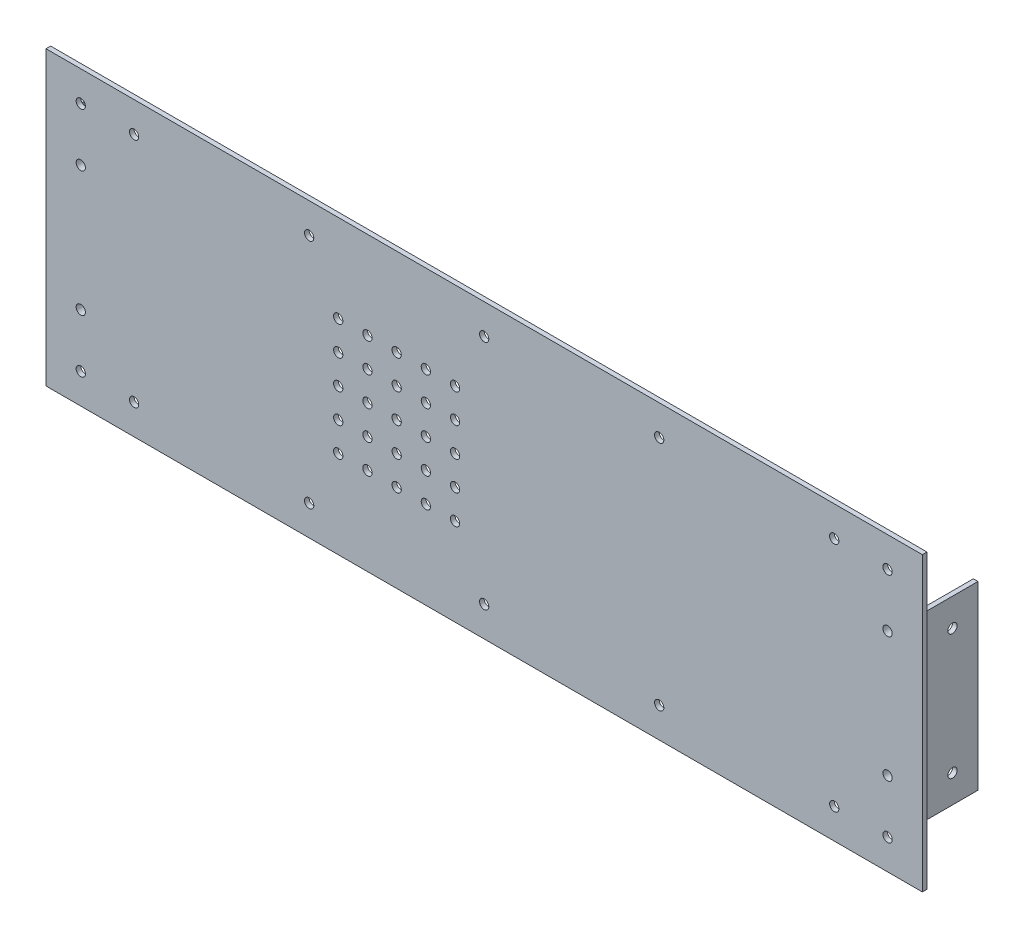
SolidWorks part; units mm, degrees
ref_plane "Plan de face" through (0, 0, 0) normal (0, 0, 1) x (1, 0, 0)
ref_plane "Plan de dessus" through (0, 0, 0) normal (0, 1, 0) x (1, 0, 0)
ref_plane "Plan de droite" through (0, 0, 0) normal (1, 0, 0) x (0, 0, -1)
sketch "Esquisse1" plane through (0, 0, 0) normal (0, 0, 1) x (1, 0, 0)
  line L1 (-120.1017, 81.1475) -> (179.8983, 81.1475)
  line L2 (-120.1017, 81.1475) -> (-120.1017, -18.8525)
  line L3 (-120.1017, -18.8525) -> (179.8983, -18.8525)
  line L4 (179.8983, 81.1475) -> (179.8983, -18.8525)
  dimension "D1" = 300
  dimension "D2" = 100
extrude "Boss.-Extru.1" add sketch "Esquisse1" along normal blind 1.5875
sketch "Esquisse2" plane through (0, 0, 0) normal (0, 0, -1) x (-1, 0, 0)
  line L1 (99.4642, 62.0975) -> (118.5142, 62.0975)
  line L2 (99.4642, 62.0975) -> (99.4642, 0.1975)
  line L3 (99.4642, 0.1975) -> (118.5142, 0.1975)
  line L4 (118.5142, 62.0975) -> (118.5142, 0.1975)
  line L5 (-178.3108, 62.0975) -> (-159.2608, 62.0975)
  line L6 (-178.3108, 62.0975) -> (-178.3108, 0.1975)
  line L7 (-178.3108, 0.1975) -> (-159.2608, 0.1975)
  line L8 (-159.2608, 62.0975) -> (-159.2608, 0.1975)
  line L10 (-179.8983, 81.1475) -> (120.1017, 81.1475) construction
  line L11 (-159.2608, 62.0975) -> (-159.2608, 81.1475) construction
  line L12 (-159.2608, 0.1975) -> (-159.2608, -18.8525) construction
  line L13 (120.1017, -18.8525) -> (-179.8983, -18.8525) construction
  line L14 (120.1017, 81.1475) -> (120.1017, -18.8525) construction
  line L15 (-179.8983, -18.8525) -> (-179.8983, 81.1475) construction
  dimension "D1" = 19.05
  dimension "D2" = 19.05
  dimension "D3" = 1.5875
  dimension "D4" = 1.5875
extrude "Boss.-Extru.2" add sketch "Esquisse2" along normal blind 1.5875
sketch "Esquisse3" plane through (0, 0, -1.5875) normal (0, 0, -1) x (-1, 0, 0)
  line L0 (118.5142, 0.1975) -> (118.5142, 62.0975) construction
  line L1 (-178.3108, 62.0975) -> (-176.7233, 62.0975)
  line L2 (-178.3108, 62.0975) -> (-178.3108, 0.1975)
  line L3 (-178.3108, 0.1975) -> (-176.7233, 0.1975)
  line L4 (-176.7233, 62.0975) -> (-176.7233, 0.1975)
  line L5 (116.9267, 62.0975) -> (118.5142, 62.0975)
  line L6 (116.9267, 62.0975) -> (116.9267, 0.1975)
  line L7 (116.9267, 0.1975) -> (118.5142, 0.1975)
  line L8 (118.5142, 62.0975) -> (118.5142, 0.1975)
  line L9 (118.5142, 62.0975) -> (99.4642, 62.0975) construction
  line L10 (99.4642, 0.1975) -> (118.5142, 0.1975) construction
  line L11 (-178.3108, 62.0975) -> (-178.3108, 0.1975) construction
  line L12 (-159.2608, 62.0975) -> (-178.3108, 62.0975) construction
  line L13 (-178.3108, 0.1975) -> (-159.2608, 0.1975) construction
  dimension "D1" = 1.5875
extrude "Boss.-Extru.3" add sketch "Esquisse3" along normal blind 17.4625
sketch "Esquisse4" plane through (0, 0, -1.5875) normal (0, 0, -1) x (-1, 0, 0)
  line L0 (-176.7233, 14.7337) -> (-159.2608, 14.7337) construction
  line L1 (-176.7233, 0.1975) -> (-176.7233, 62.0975) construction
  line L2 (-159.2608, 0.1975) -> (-159.2608, 62.0975) construction
  line L3 (99.4642, 15.3602) -> (116.9267, 15.3602) construction
  line L4 (99.4642, 62.0975) -> (99.4642, 0.1975) construction
  line L5 (116.9267, 62.0975) -> (116.9267, 0.1975) construction
  line L6 (-167.9921, 52.5725) -> (-167.9921, 9.7225) construction
  line L7 (-159.2608, 62.0975) -> (-176.7233, 62.0975) construction
  circle A0 centre (-167.9921, 52.5725) radius 1.5875
  circle A1 centre (-167.9921, 9.7225) radius 1.5875
  circle A2 centre (108.1954, 52.5725) radius 1.5875
  circle A3 centre (108.1954, 9.7225) radius 1.5875
  point P8 (108.1954, 15.3602)
  point P9 (-167.9921, 14.7337)
  point P22 (-167.9921, 31.1475)
  point P23 (-176.7233, 31.1475)
  dimension "D1" = 3.175
  dimension "D2" = 9.525
extrude "Enlèv. mat.-Extru.1" cut sketch "Esquisse4" against normal up to next
sketch "Esquisse5" plane through (0, 0, 1.5875) normal (0, 0, 1) x (1, 0, 0)
  line L0 (-120.1017, -18.8525) -> (179.8983, -18.8525) construction
  line L1 (-120.1017, 81.1475) -> (-120.1017, -18.8525) construction
  line L2 (179.8983, -18.8525) -> (179.8983, 81.1475) construction
  line L3 (-30.0204, -8.5337) -> (89.8171, -8.5337) construction
  line L4 (-120.1017, 31.1475) -> (179.8983, 31.1475) construction
  line L5 (-99.4642, 62.0975) -> (-99.4642, 0.1975) construction
  line L6 (159.2608, 0.1975) -> (159.2608, 62.0975) construction
  line L7 (149.7358, -8.5337) -> (29.8983, -8.5337) construction
  circle A0 centre (-108.1954, -8.5337) radius 1.5875
  circle A1 centre (-89.9392, -8.5337) radius 1.5875
  circle A2 centre (-30.0204, -8.5337) radius 1.5875
  circle A3 centre (29.8983, -8.5337) radius 1.5875
  circle A4 centre (89.8171, -8.5337) radius 1.5875
  circle A5 centre (149.7358, -8.5337) radius 1.5875
  circle A6 centre (167.9921, -8.5337) radius 1.5875
  circle A7 centre (167.9921, 70.8288) radius 1.5875
  circle A8 centre (149.7358, 70.8288) radius 1.5875
  circle A9 centre (89.8171, 70.8288) radius 1.5875
  circle A10 centre (29.8983, 70.8288) radius 1.5875
  circle A11 centre (-30.0204, 70.8288) radius 1.5875
  circle A12 centre (-89.9392, 70.8288) radius 1.5875
  circle A13 centre (-108.1954, 70.8288) radius 1.5875
  circle A14 centre (167.9921, 9.7225) radius 1.5875 construction
  circle A15 centre (167.9921, 9.7225) radius 1.5875 construction
  circle A16 centre (-108.1954, 9.7225) radius 1.5875 construction
  circle A17 centre (-108.1954, 9.7225) radius 1.5875 construction
  point P14 (29.8983, -8.5337)
  point P22 (29.8983, -18.8525)
  dimension "D1" = 3.175
  dimension "D2" = 10.3187
  dimension "D3" = 9.525
  dimension "D4" = 9.525
extrude "Enlèv. mat.-Extru.2" cut sketch "Esquisse5" against normal up to next
sketch "Esquisse7" plane through (176.7233, 0, 0) normal (-1, 0, 0) x (0, 0, 1)
  line L0 (-1.5875, 54.16) -> (-1.5875, 50.985) construction
  line L1 (-1.5875, 11.31) -> (-1.5875, 8.135) construction
  line L2 (-1.5875, 54.16) -> (-1.5875, 50.985) construction
  line L3 (-1.5875, 11.31) -> (-1.5875, 8.135) construction
  line L4 (-19.05, 16.0041) -> (-1.5875, 16.0041) construction
  line L5 (-19.05, 0.1975) -> (-19.05, 62.0975) construction
  line L6 (-1.5875, 0.1975) -> (-1.5875, 62.0975) construction
  circle A0 centre (-10.3187, 52.5725) radius 1.5875
  circle A1 centre (-10.3187, 9.7225) radius 1.5875
  point P9 (-1.5875, 52.5725)
  point P10 (-1.5875, 9.7225)
  point P17 (-10.3187, 16.0041)
  dimension "D1" = 3.175
extrude "Enlèv. mat.-Extru.4" cut sketch "Esquisse7" against normal through all both and the other way through all
sketch "Esquisse8" plane through (0, 0, 1.5875) normal (0, 0, 1) x (1, 0, 0)
  line L0 (-30.0204, 70.8288) -> (29.8983, 70.8288) construction
  line L1 (-120.1017, 81.1475) -> (-120.1017, -18.8525) construction
  circle A0 centre (-20.061, 11.1475) radius 1.5875
  circle A1 centre (-10.061, 11.1475) radius 1.5875
  circle A2 centre (-0.061, 11.1475) radius 1.5875
  circle A3 centre (9.939, 11.1475) radius 1.5875
  circle A4 centre (19.939, 11.1475) radius 1.5875
  circle A5 centre (-10.061, 21.1475) radius 1.5875
  circle A6 centre (-0.061, 21.1475) radius 1.5875
  circle A7 centre (9.939, 21.1475) radius 1.5875
  circle A8 centre (19.939, 21.1475) radius 1.5875
  circle A9 centre (-10.061, 31.1475) radius 1.5875
  circle A10 centre (-0.061, 31.1475) radius 1.5875
  circle A11 centre (9.939, 31.1475) radius 1.5875
  circle A12 centre (19.939, 31.1475) radius 1.5875
  circle A13 centre (-10.061, 41.1475) radius 1.5875
  circle A14 centre (-0.061, 41.1475) radius 1.5875
  circle A15 centre (9.939, 41.1475) radius 1.5875
  circle A16 centre (19.939, 41.1475) radius 1.5875
  circle A17 centre (-10.061, 51.1475) radius 1.5875
  circle A18 centre (-0.061, 51.1475) radius 1.5875
  circle A19 centre (9.939, 51.1475) radius 1.5875
  circle A20 centre (19.939, 51.1475) radius 1.5875
  circle A21 centre (-20.061, 21.1475) radius 1.5875
  circle A22 centre (-20.061, 31.1475) radius 1.5875
  circle A23 centre (-20.061, 41.1475) radius 1.5875
  circle A24 centre (-20.061, 51.1475) radius 1.5875
  point P2 (-120.1017, 31.1475)
  point P8 (-0.061, 70.8288)
  dimension "D1" = 3.175
  dimension "D4" = 5
extrude "Enlèv. mat.-Extru.5" cut sketch "Esquisse8" against normal up to next (1.5875 mm away)
